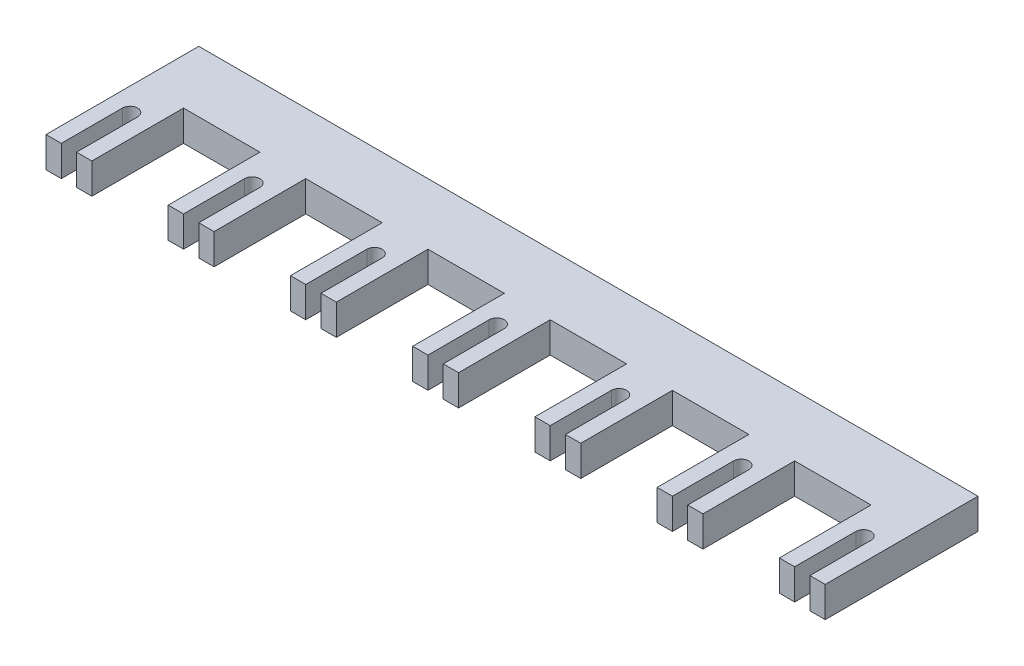
SolidWorks part; units mm, degrees
ref_plane "Front Plane" through (0, 0, 0) normal (0, 0, 1) x (1, 0, 0)
ref_plane "Top Plane" through (0, 0, 0) normal (0, 1, 0) x (1, 0, 0)
ref_plane "Right Plane" through (0, 0, 0) normal (1, 0, 0) x (0, 0, -1)
sketch "Sketch1" plane through (0, 0, 0) normal (0, 1, 0) x (1, 0, 0)
  line L0 (0, 0) -> (0, 20)
  line L1 (0, 20) -> (5, 20) construction
  line L2 (5, 20) -> (5, 0)
  line L3 (5, 0) -> (10, 0)
  line L4 (10, 0) -> (10, 30)
  line L6 (-5, 30) -> (-5, 0)
  line L7 (-5, 0) -> (0, 0)
  line L8 (35, 0) -> (40, 0)
  line L9 (40, 0) -> (40, 20)
  line L10 (45, 20) -> (45, 0)
  line L11 (45, 0) -> (50, 0)
  line L12 (50, 0) -> (50, 30)
  line L14 (35, 30) -> (35, 0)
  line L15 (75, 0) -> (80, 0)
  line L16 (80, 0) -> (80, 20)
  line L17 (85, 20) -> (85, 0)
  line L18 (85, 0) -> (90, 0)
  line L19 (90, 0) -> (90, 30)
  line L21 (75, 30) -> (75, 0)
  line L22 (115, 0) -> (120, 0)
  line L23 (120, 0) -> (120, 20)
  line L24 (125, 20) -> (125, 0)
  line L25 (125, 0) -> (130, 0)
  line L26 (130, 0) -> (130, 30)
  line L28 (115, 30) -> (115, 0)
  line L29 (155, 0) -> (160, 0)
  line L30 (160, 0) -> (160, 20)
  line L31 (165, 20) -> (165, 0)
  line L32 (165, 0) -> (170, 0)
  line L33 (170, 0) -> (170, 30)
  line L35 (155, 30) -> (155, 0)
  line L36 (195, 0) -> (200, 0)
  line L37 (200, 0) -> (200, 20)
  line L38 (205, 20) -> (205, 0)
  line L39 (205, 0) -> (210, 0)
  line L40 (210, 0) -> (210, 30)
  line L42 (195, 30) -> (195, 0)
  line L43 (90, 30) -> (115, 30)
  line L44 (10, 30) -> (35, 30)
  line L45 (-5, 30) -> (-5, 50)
  line L46 (-5, 50) -> (250, 50)
  line L48 (235, 0) -> (240, 0)
  line L49 (240, 0) -> (240, 20)
  line L50 (245, 20) -> (245, 0)
  line L51 (245, 0) -> (250, 0)
  line L52 (130, 30) -> (155, 30)
  line L53 (170, 30) -> (195, 30)
  line L54 (250, 0) -> (250, 30)
  line L55 (50, 30) -> (75, 30)
  line L56 (235, 30) -> (235, 0)
  line L57 (250, 30) -> (250, 50)
  line L58 (210, 30) -> (235, 30)
  arc A0 (5, 20) -> (0, 20) centre (2.5, 20) ccw
  arc A1 (45, 20) -> (40, 20) centre (42.5, 20) ccw
  arc A2 (85, 20) -> (80, 20) centre (82.5, 20) ccw
  arc A3 (125, 20) -> (120, 20) centre (122.5, 20) ccw
  arc A4 (165, 20) -> (160, 20) centre (162.5, 20) ccw
  arc A5 (205, 20) -> (200, 20) centre (202.5, 20) ccw
  arc A6 (245, 20) -> (240, 20) centre (242.5, 20) ccw
  dimension "D1" = 20
  dimension "D2" = 5
  dimension "D3" = 5
  dimension "D4" = 30
  dimension "D6" = 40
  dimension "D7" = 20
  dimension "D5" = 7
extrude "Boss-Extrude1" add sketch "Sketch1" along normal blind 10
